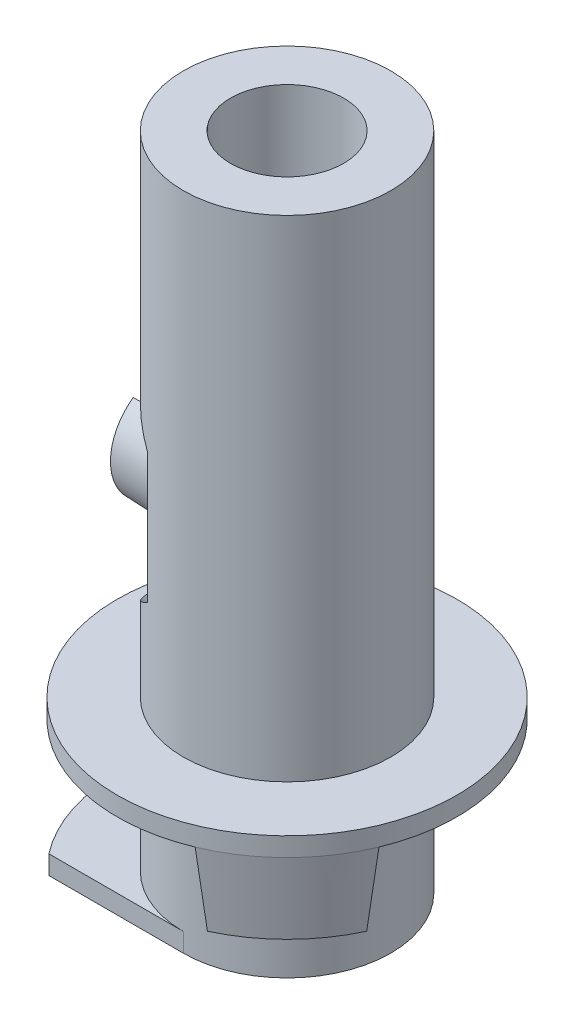
SolidWorks part; units mm, degrees
ref_plane "前视基准面" through (0, 0, 0) normal (0, 0, 1) x (1, 0, 0)
ref_plane "上视基准面" through (0, 0, 0) normal (0, 1, 0) x (1, 0, 0)
ref_plane "右视基准面" through (0, 0, 0) normal (1, 0, 0) x (0, 0, -1)
sketch "草图1" plane through (0, 0, 0) normal (0, 1, 0) x (1, 0, 0)
  circle A0 centre (0, 0) radius 4.5
  dimension "D1" = 9
extrude "凸台-拉伸1" add sketch "草图1" along normal blind 17.5
sketch "草图2" plane through (0, 0, 0) normal (0, 0, 1) x (1, 0, 0)
  line L0 (0, 0) -> (0, -50000) construction
  line L1 (-4.5, 0) -> (4.5, 0) construction
  line L2 (4.5, 17.5) -> (2.75, 17.5)
  line L3 (4.5, 17.5) -> (4.5, 4.5)
  line L4 (4.5, 4.5) -> (2.75, 4.5)
  line L5 (2.75, 17.5) -> (2.75, 4.5)
  dimension "D1" = 5.5
  dimension "D2" = 4.5
revolve "切除-旋转1" cut sketch "草图2" angle 360 about L0
sketch "草图3" plane through (0, 0, 0) normal (0, 0, 1) x (1, 0, 0)
  line L0 (0, 0) -> (0, 50000) construction
  line L1 (4.5, 0) -> (4.5, 4.5) construction
  line L2 (4.5, 0.5) -> (2.75, 0.5)
  line L3 (4.5, 0.5) -> (4.5, 4)
  line L4 (4.5, 4) -> (2.75, 4)
  line L5 (2.75, 0.5) -> (2.75, 4)
  line L6 (4.5, 4.5) -> (-4.5, 4.5) construction
  line L7 (-4.5, 0) -> (4.5, 0) construction
  line L8 (2.75, 4.5) -> (2.75, 17.5) construction
  dimension "D1" = 0.5
  dimension "D2" = 0.5
revolve "切除-旋转2" cut sketch "草图3" angle 360 about L0
sketch "草图4" plane through (0, 0, 0) normal (0, -1, 0) x (1, 0, 0)
  line L0 (0, 2.75) -> (-3.562, 2.75)
  line L1 (0, -2.75) -> (-3.562, -2.75)
  arc A0 (-3.562, -2.75) -> (-3.562, 2.75) centre (0, 0) ccw
  arc A1 (0, -2.75) -> (0, 2.75) centre (0, 0) ccw
  circle A2 centre (0, 0) radius 2.75 construction
  circle A3 centre (0, 0) radius 4.5 construction
extrude "切除-拉伸1" cut sketch "草图4" against normal up to surface (0.5 mm away) up to face at (0, 0.5, -4.5)
sketch "草图6" plane through (0, 4, 0) normal (0, -1, 0) x (1, 0, 0)
  line L0 (0, 0) -> (35355.3391, 35355.3391) construction
  line L1 (4.95, 0) -> (-4.95, 0) construction
  line L3 (1.3394, 3.2336) -> (1.7221, 4.1575)
  line L4 (3.2336, 1.3394) -> (4.1575, 1.7221)
  arc A3 (4.1575, 1.7221) -> (1.7221, 4.1575) centre (0, 0) ccw
  circle A4 centre (0, 0) radius 4.5 construction
  arc A5 (3.2336, 1.3394) -> (1.3394, 3.2336) centre (0, 0) ccw
  dimension "D2" = 1
  dimension "D4" = 1
  dimension "D1" = 45
  dimension "D3" = 45
extrude "凸台-拉伸2" add sketch "草图6" along normal blind 2 draft 5
ref_plane "基准面1" through (-2.75, 0, 0) normal (1, 0, 0) x (0, 0, -1)
sketch "草图7" plane through (-2.75, 0, 0) normal (1, 0, 0) x (0, 0, -1)
  line L0 (0, 4.95) -> (0, -4.95) construction
  line L1 (2.75, 17.5) -> (-2.75, 17.5) construction
  circle A0 centre (0, 9) radius 3
  dimension "D1" = 6
  dimension "D2" = 8.5
extrude "切除-拉伸2" cut sketch "草图7" along normal blind 1.5
sketch "草图8" plane through (-1.25, 0, 0) normal (-1, 0, 0) x (0, 0, 1)
  line L0 (0, -4.95) -> (0, 4.95) construction
  circle A0 centre (0, 9) radius 1.5
  arc A1 (2.4495, 10.7321) -> (-2.4495, 10.7321) centre (0, 9) ccw construction
  dimension "D1" = 3
extrude "凸台-拉伸3" add sketch "草图8" along normal blind 2 draft 2
hole_wizard "孔1" positions "草图11" profile "草图13" legacy end condition through all
sketch "草图11" plane through (0, 17.5, 0) normal (0, 1, 0) x (1, 0, 0)
  point P0 (0, 0)
sketch "草图13" plane through (0, 17.5, 0) normal (1, 0, 0) x (0, 0, 1)
  line L0 (0, 0) -> (0, 17.5)
  line L1 (0, 17.5) -> (1, 17.5)
  line L2 (1, 17.5) -> (1, 13)
  line L3 (1, 13) -> (1.5, 13)
  line L4 (1.5, 13) -> (1.5, 0)
  line L5 (1.5, 0) -> (0, 0)
  line L6 (0, 110) -> (0, -10) construction
  dimension "直径" = 2
  dimension "深度" = 17.5
  dimension "柱坑直径" = 3
  dimension "柱坑深度" = 13
sketch "草图16" plane through (-3.25, 0, 0) normal (-1, 0, 0) x (0, 0, 1)
  line L0 (-0.8292, 10.25) -> (-0.8292, 11.8831) construction
  line L1 (-0.8292, 10.4913) -> (0.8292, 10.4913)
  line L2 (-0.8292, 10.4913) -> (-0.8292, 7.5087)
  line L3 (-0.8292, 7.5087) -> (0.8292, 7.5087)
  line L4 (0.8292, 10.4913) -> (0.8292, 7.5087)
  line L5 (0.8292, 7.75) -> (0.8292, 6.1169) construction
  spline S1 degree 3 poles (0.8292, 10.25) (0.7155, 10.3222) (0.5884, 10.3825) (0.3058, 10.4679) (0.1551, 10.4911) (-0.1524, 10.4914) (-0.305, 10.468) (-0.5862, 10.3833) (-0.7153, 10.3224) (-0.8292, 10.25) knots 0 0 0 0 0.25 0.25 0.5 0.5 0.75 0.75 1 1 1 1 construction
  spline S2 degree 3 poles (-0.8292, 7.75) (-0.7155, 7.6778) (-0.5884, 7.6175) (-0.3058, 7.5321) (-0.1551, 7.5089) (0.1524, 7.5086) (0.305, 7.532) (0.5862, 7.6167) (0.7153, 7.6776) (0.8292, 7.75) knots 0 0 0 0 0.25 0.25 0.5 0.5 0.75 0.75 1 1 1 1 construction
extrude "切除-拉伸4" cut sketch "草图16" against normal up to surface (2 mm away)
